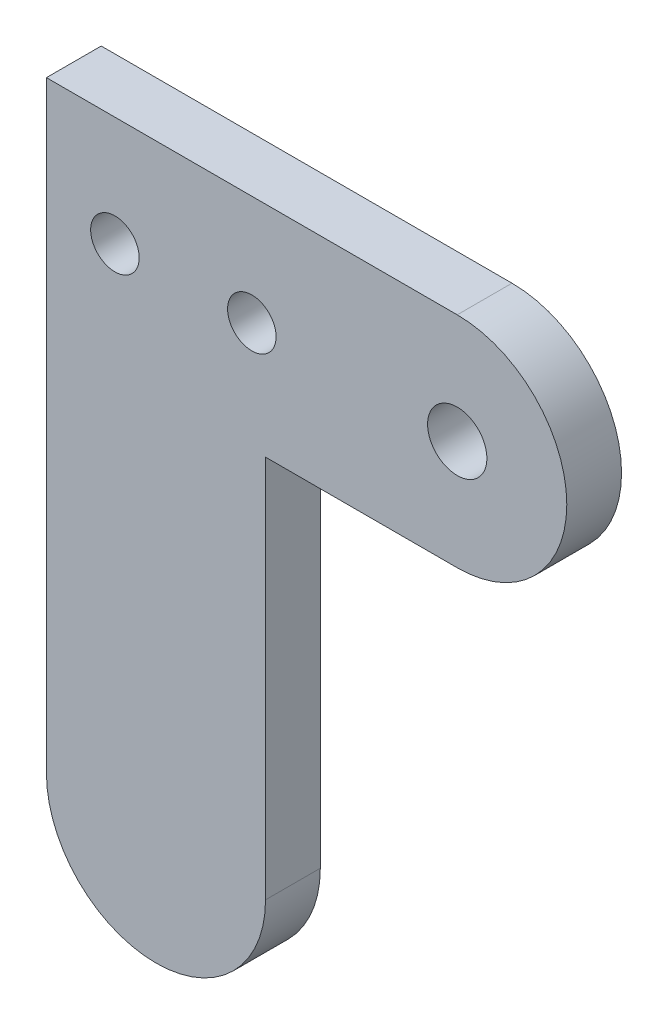
SolidWorks part; units mm, degrees
ref_plane "Front Plane" through (0, 0, 0) normal (0, 0, 1) x (1, 0, 0)
ref_plane "Top Plane" through (0, 0, 0) normal (0, 1, 0) x (1, 0, 0)
ref_plane "Right Plane" through (0, 0, 0) normal (1, 0, 0) x (0, 0, -1)
sketch "Sketch1" plane through (0, 0, 0) normal (0, 0, 1) x (1, 0, 0)
  line L0 (0, 10.16) -> (0, -10.16)
  line L2 (38.1, 10.16) -> (0, 10.16)
  line L3 (38.1, -10.16) -> (20.32, -10.16)
  line L4 (20.32, -10.16) -> (20.32, -45.72)
  line L5 (0, -45.72) -> (0, -10.16)
  arc A0 (38.1, -10.16) -> (38.1, 10.16) centre (38.1, 0) ccw
  arc A1 (20.32, -45.72) -> (0, -45.72) centre (10.16, -45.72) cw
  point P6 (0, 0)
  dimension "D3" = 20.32
  dimension "D4" = 35.56
  dimension "D1" = 20.32
  dimension "D2" = 38.1
extrude "Boss-Extrude1" add sketch "Sketch1" along normal blind 5.08
hole_wizard "M5 Clearance Hole1" positions "Sketch2" profile "Sketch3" hole size "M5" standard "ANSI Metric" end condition through all
sketch "Sketch2" plane through (0, 0, 5.08) normal (0, 0, 1) x (1, 0, 0)
  arc A0 (38.1, -10.16) -> (38.1, 10.16) centre (38.1, 0) ccw construction
  point P0 (38.1, 0)
sketch "Sketch3" plane through (38.1, 0, 5.08) normal (1, 0, 0) x (0, -1, 0)
  line L0 (0, 0) -> (0, 5.08)
  line L1 (0, 5.08) -> (2.75, 5.08)
  line L2 (2.75, 5.08) -> (2.75, 0)
  line L5 (2.75, 0) -> (0, 0)
  line L11 (0, -6.35) -> (0, 107.95) construction
  dimension "Thru Hole Dia." = 5.5
  dimension "Thru Hole Depth" = 5.08
hole_wizard "M4 Clearance Hole1" positions "Sketch4" profile "Sketch5" hole size "M4" standard "ANSI Metric" end condition through all
sketch "Sketch4" plane through (0, 0, 5.08) normal (0, 0, 1) x (1, 0, 0)
  line L6 (0, 10.16) -> (0, -45.72) construction
  point P0 (19.05, -0.0163)
  point P2 (6.35, -0.0163)
  dimension "D1" = 12.7
  dimension "D2" = 6.35
sketch "Sketch5" plane through (19.05, -0.0163, 5.08) normal (1, 0, 0) x (0, -1, 0)
  line L0 (0, 0) -> (0, 5.08)
  line L1 (0, 5.08) -> (2.25, 5.08)
  line L2 (2.25, 5.08) -> (2.25, 0)
  line L5 (2.25, 0) -> (0, 0)
  line L11 (0, -6.35) -> (0, 107.95) construction
  dimension "Thru Hole Dia." = 4.5
  dimension "Thru Hole Depth" = 5.08
